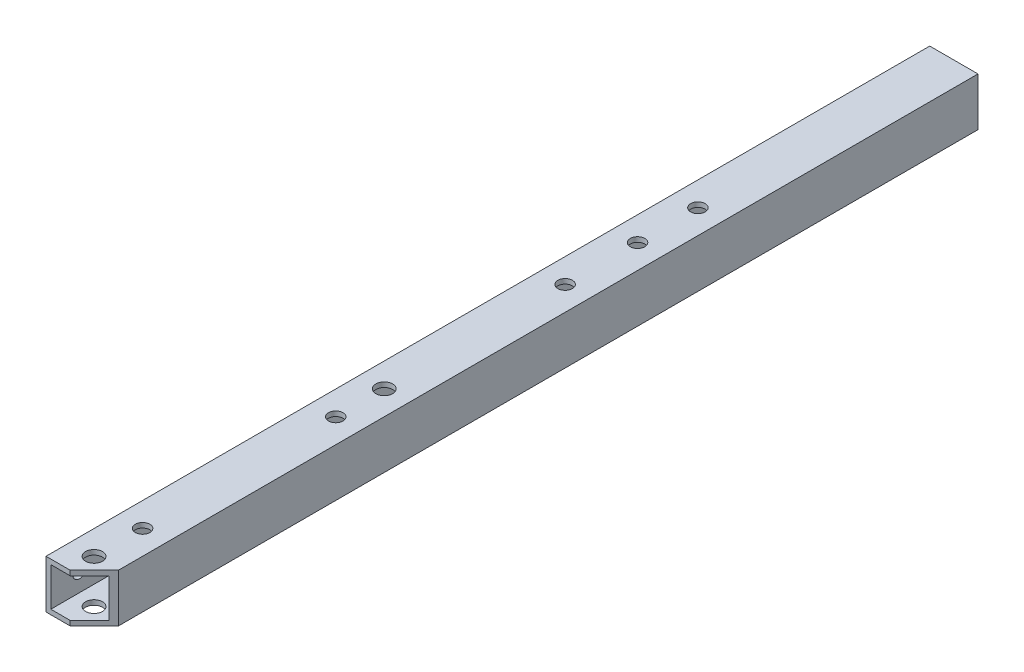
SolidWorks part; units mm, degrees
material "6063-O"
ref_plane "前视基准面" through (0, 0, 0) normal (0, 0, 1) x (1, 0, 0)
ref_plane "上视基准面" through (0, 0, 0) normal (0, 1, 0) x (1, 0, 0)
ref_plane "右视基准面" through (0, 0, 0) normal (1, 0, 0) x (0, 0, -1)
other "Configuration Table"
sketch "草图1" plane through (0, 0, 0) normal (0, 0, 1) x (1, 0, 0)
  line L1 (-5, 5) -> (5, 5)
  line L2 (-5, 5) -> (-5, -5)
  line L3 (-5, -5) -> (5, -5)
  line L4 (5, 5) -> (5, -5)
  line L5 (-5, 5) -> (5, -5) construction
  line L6 (-5, -5) -> (5, 5) construction
  point P4 (0, 0)
  dimension "D1" = 10
  dimension "D2" = 10
extrude "拉伸-薄壁1" add sketch "草图1" along normal blind 183 thin
sketch "草图2" plane through (0, 5, 0) normal (0, 1, 0) x (1, 0, 0)
  line L0 (0, -183) -> (0, 0) construction
  line L1 (5, -183) -> (-5, -183) construction
  line L2 (5, 0) -> (-5, 0) construction
  line L4 (0, -73) -> (5, -73) construction
  line L7 (-30.052, -148) -> (12.448, -148) construction
  line L8 (-30.052, -148) -> (0, -117.948) construction
  line L9 (0, -117.948) -> (0, -128) construction
  line L11 (5, -183) -> (5, 0) construction
  line L12 (5, -178) -> (5, -183)
  line L13 (5, -183) -> (-5, -183)
  line L14 (5, -178) -> (0, -183)
  circle A6 centre (-30.052, -148) radius 42.5 construction
  circle A7 centre (0, -117.948) radius 1.75
  circle A8 centre (0, -128) radius 1.5
  circle A9 centre (0, -168) radius 1.5
  circle A10 centre (0, -178.052) radius 1.75
  circle A11 centre (0, -53) radius 1.5
  circle A12 centre (0, -65.5) radius 1.5
  circle A13 centre (0, -80.5) radius 1.5
  line M7 (5, -183) -> (5, 0)
  dimension "D1" = 85
  dimension "D4" = 40
  dimension "D6" = 35
  dimension "D7" = 45
  dimension "D8" = 53
  dimension "D2" = 3.5
  dimension "D5" = 3
  dimension "D10" = 15
  dimension "D3" = 45
  dimension "D9" = 73
extrude "切除-拉伸1" cut sketch "草图2" against normal through all contours L14 L13 M7 | A10 | A9 | A8 | A7 | A13 | A12 | A11
sketch "草图4" plane through (-5, 0, 0) normal (-1, 0, 0) x (0, 0, 1)
  line L0 (183, 0) -> (177, 0) construction
  line L2 (183, 5) -> (183, -5) construction
  circle A0 centre (177, 0) radius 1.5
  dimension "D1" = 3
  dimension "D2" = 6
extrude "切除-拉伸2" cut sketch "草图4" against normal blind 5
